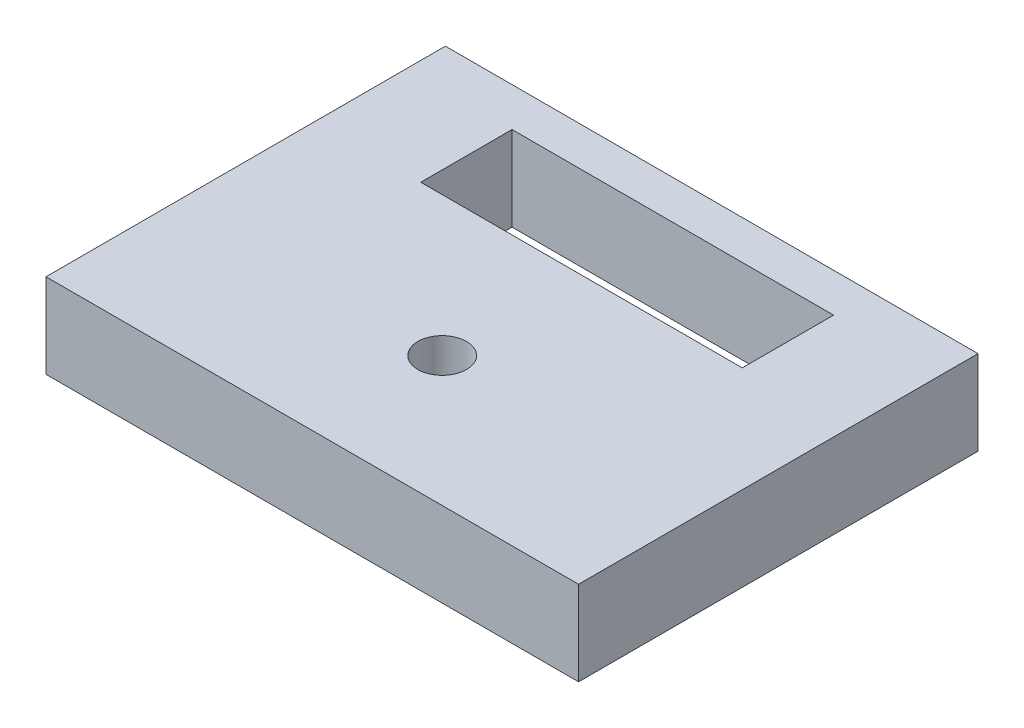
SolidWorks part; units mm, degrees
ref_plane "Front Plane" through (0, 0, 0) normal (0, 0, 1) x (1, 0, 0)
ref_plane "Top Plane" through (0, 0, 0) normal (0, 1, 0) x (1, 0, 0)
ref_plane "Right Plane" through (0, 0, 0) normal (1, 0, 0) x (0, 0, -1)
sketch "Sketch1" plane through (0, 0, 0) normal (0, 1, 0) x (1, 0, 0)
  line L0 (-20, -15) -> (-20, 15)
  line L1 (-20, -15) -> (20, -15)
  line L2 (-20, 15) -> (20, 15)
  line L3 (20, -15) -> (20, 15)
  line L4 (-20, -15) -> (20, 15) construction
  line L5 (-20, 15) -> (20, -15) construction
  point P1 (0, 0)
  dimension "D1" = 30
  dimension "D2" = 40
extrude "Boss-Extrude1" add sketch "Sketch1" along normal blind 6.35
sketch "Sketch2" plane through (0, 6.35, 0) normal (0, 1, 0) x (1, 0, 0)
  line L0 (-12.074, 5.221) -> (-12.074, 12.079)
  line L1 (-12.074, 5.221) -> (12.074, 5.221)
  line L2 (-12.074, 12.079) -> (12.074, 12.079)
  line L3 (12.074, 5.221) -> (12.074, 12.079)
  line L4 (-12.074, 5.221) -> (12.074, 12.079) construction
  line L5 (-12.074, 12.079) -> (12.074, 5.221) construction
  line L6 (20, 15) -> (-20, 15) construction
  point P1 (0, 8.65)
  dimension "D1" = 6.858
  dimension "D2" = 24.148
  dimension "D3" = 6.35
extrude "Cut-Extrude1" cut sketch "Sketch2" against normal through all
sketch "Sketch3" plane through (0, 6.35, 0) normal (0, 1, 0) x (1, 0, 0)
  line L0 (-12.074, 5.221) -> (12.074, 5.221) construction
  point P0 (0, -5.2438)
  dimension "D1" = 10.4648
hole_wizard "#6 Clearance Hole1" positions "Sketch5" profile "Sketch4" hole size "#6" standard "ANSI Inch" end condition through all
sketch "Sketch5" plane through (0, 6.35, 0) normal (0, 1, 0) x (1, 0, 0)
  point P0 (0, -5.2438)
sketch "Sketch4" plane through (0, 6.35, 5.2438) normal (1, 0, 0) x (0, 0, 1)
  line L0 (0, 0) -> (0, 6.35)
  line L1 (0, 6.35) -> (1.8288, 6.35)
  line L2 (1.8288, 6.35) -> (1.8288, 0)
  line L5 (1.8288, 0) -> (0, 0)
  line L11 (0, -6.35) -> (0, 107.95) construction
  dimension "Thru Hole Dia." = 3.6576
  dimension "Thru Hole Depth" = 6.35
